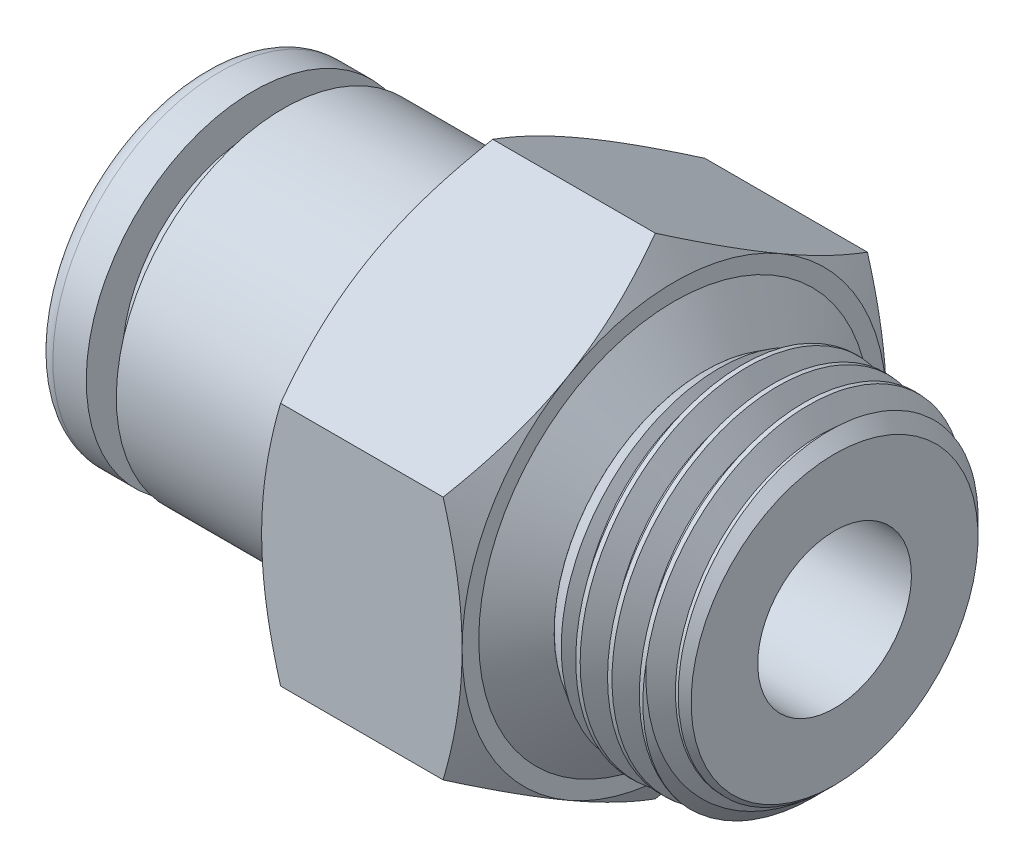
SolidWorks part; units mm, degrees
ref_plane "Front Plane" through (0, 0, 0) normal (0, 0, 1) x (1, 0, 0)
ref_plane "Top Plane" through (0, 0, 0) normal (0, 1, 0) x (1, 0, 0)
ref_plane "Right Plane" through (0, 0, 0) normal (1, 0, 0) x (0, 0, -1)
sketch "Sketch0" plane through (0, 0, 0) normal (0, 0, -1) x (-1, 0, 0)
  line L0 (0, 0) -> (-18.9, 0) construction
  line L1 (0, 5) -> (0, -5) construction
  line L2 (-13.3, 3.175) -> (-13.3, -3.175) construction
  line L3 (-14.1, 5.1435) -> (-14.1, -5.1435) construction
  line L4 (-9.45, 6.35) -> (-9.45, -6.35) construction
  line L5 (-18.9, 2.3) -> (-18.9, -2.3) construction
  point P3 (-13.3, 0)
  point P11 (-9.45, 0)
  point P16 (-14.1, 0)
sketch "Sketch1" plane through (0, 0, 0) normal (0, 0, -1) x (-1, 0, 0)
  line L0 (0, 4.5) -> (0, 3.675)
  line L1 (-0.5, 5) -> (-1.5, 5)
  line L2 (-1.5, 5) -> (-1.5, 3.925)
  line L3 (-1.5, 3.925) -> (-2.4, 3.925)
  line L4 (-2.4, 3.925) -> (-2.4, 5)
  line L5 (-2.4, 5) -> (-14.1, 5)
  line L6 (-14.1, 5.1435) -> (-14.1, -5.1435) construction
  line L7 (0, 0) -> (-18.9, 0) construction
  line L8 (-14.1, 0) -> (-9.45, 0) construction
  line L10 (0, 0) -> (-18.9, 0) construction
  line L11 (-9.45, 3.175) -> (-0.5, 3.175)
  line L12 (0, 5) -> (0, -5) construction
  line L15 (-9.45, 0) -> (-14.1, 0)
  line L16 (-14.1, 0) -> (-14.1, 5)
  line L17 (-9.45, 0) -> (-9.45, 3.175)
  line L18 (-9.45, 6.35) -> (-9.45, -6.35) construction
  arc A0 (0, 4.5) -> (-0.5, 5) centre (-0.5, 4.5) ccw
  arc A1 (-0.5, 3.175) -> (0, 3.675) centre (-0.5, 3.675) ccw
  point P15 (0, 5)
  point P19 (0, 5)
  point P25 (0, 3.175)
  dimension "R" = 0.5
  dimension "D1" = 1.5
  dimension "D3" = 7.85
  dimension "D2" = 0.9
revolve "Revolve2" add sketch "Sketch1" angle 360 about L10
ref_plane "Plane1" through (14.1, 0, 0) normal (1, 0, 0) x (0, 0, -1)
sketch "Sketch2" plane through (14.1, 0, 0) normal (1, 0, 0) x (0, 0, -1)
  circle A0 centre (0, 0) radius 5.1435
  point P5 (0, -5.1435)
extrude "Extrude1" add sketch "Sketch2" along normal up to vertex (4.8 mm away) draft 1.783 separate body up to point (18.9, 0, 0)
sketch "Sketch3" plane through (18.9, 0, 0) normal (1, 0, 0) x (0, 0, -1)
  circle A0 centre (0, 0) radius 4.9941 construction
  circle A1 centre (0, 0) radius 4.9941
curve "Helix/Spiral1" parameters "Height"=5.7236, "Pitch"=0.9236
sketch "Sketch4" plane through (0, 0, 0) normal (0, 0, -1) x (-1, 0, 0)
  line L0 (-19.7659, 5.094) -> (-19.3041, 4.2941) construction
  line L1 (-19.3041, 4.2941) -> (-18.8423, 5.094) construction
  line L2 (-18.8423, 5.094) -> (-19.7659, 5.094) construction
  line L3 (-19.7082, 4.9941) -> (-18.9, 4.9941) construction
  line L4 (-19.3041, 5.094) -> (-19.3041, 4.9941) construction
  line L5 (-19.3041, 4.9941) -> (-19.3041, 4.3941) construction
  line L6 (-19.3041, 4.3941) -> (-19.3041, 4.2941) construction
  line L7 (-19.3618, 4.3941) -> (-19.2464, 4.3941)
  line L8 (-18.8423, 5.094) -> (-19.7082, 4.9941)
  line L9 (-18.8423, 5.094) -> (-19.2464, 4.3941)
  line L10 (-19.7082, 4.9941) -> (-19.3618, 4.3941)
  line L11 (-19.3041, 4.2941) -> (-19.3041, -4.9815) construction
  line L12 (-19.3041, -4.9815) -> (-18.3809, -5.0102) construction
  line L13 (-18.3809, -5.0102) -> (-17.4577, -5.039) construction
  line L14 (-17.4577, -5.039) -> (-16.5345, -5.0677) construction
  line L15 (-16.5345, -5.0677) -> (-15.6113, -5.0964) construction
  line L16 (-18.9, -4.9941) -> (-14.1, -5.1435) construction
  dimension "D1" = 0.9236
  dimension "D2" = 0.1155
sketch "Sketch5" plane through (18.9, 0, 0) normal (1, 0, 0) x (0, 0, -1)
  circle A0 centre (0, 0) radius 4.2941
extrude "Extrude2" cut sketch "Sketch5" against normal up to vertex (4.8 mm away) draft 45 flip side to cut up to point (14.1, 0, 0)
sweep "Cut-Sweep1" cut profiles "Sketch4" path "Helix/Spiral1"
sketch "Sketch5.5" plane through (0, 0, 0) normal (0, 0, 1) x (1, 0, 0)
  line L0 (14.1, -5.1435) -> (15.0232, -5.1148)
  line L1 (19.3041, -4.9815) -> (18.3809, -5.0102) construction
  line L2 (15.0232, -5.1148) -> (15.9464, -5.086)
  line L3 (15.9464, -5.086) -> (15.0232, -4.5148)
  line L4 (15.0232, -4.5148) -> (15.0232, -5.1148) construction
  line L5 (19.3041, 4.9941) -> (19.3041, 4.3941) construction
  line L6 (15.0232, -4.5148) -> (14.1, -4.5436)
  line L7 (14.1, -4.5436) -> (14.1, -5.1435)
  line L8 (14.1, 0) -> (19.3041, 0) construction
  line L9 (14.1, -5.1435) -> (14.1, 5.1435) construction
  line L10 (19.3041, 4.2941) -> (19.3041, -4.9815) construction
revolve "Cut-Revolve1" cut sketch "Sketch5.5" angle 360 about L8
ref_plane "Plane2" through (14.1, 0, 0) normal (1, 0, 0) x (0, 0, -1)
sketch "Sketch6" plane through (14.1, 0, 0) normal (1, 0, 0) x (0, 0, -1)
  circle A0 centre (0, 0) radius 3.175
  circle A2 centre (0, 0) radius 5.1435
  circle A3 centre (0, 0) radius 5.1435
  dimension "D1" = 0
extrude "Extrude3" add sketch "Sketch6" against normal blind 3 draft 45
sketch "Sketch7" plane through (18.9, 0, 0) normal (1, 0, 0) x (0, 0, -1)
  circle A0 centre (0, 0) radius 2.3
extrude "Extrude4" cut sketch "Sketch7" against normal through all
sketch "Sketch8" plane through (14.1, 0, 0) normal (1, 0, 0) x (0, 0, -1)
  line L1 (0, 7.3323) -> (-6.35, 3.6662)
  line L2 (-6.35, 3.6662) -> (-6.35, -3.6662)
  line L3 (-6.35, -3.6662) -> (0, -7.3323)
  line L4 (0, -7.3323) -> (6.35, -3.6662)
  line L5 (6.35, -3.6662) -> (6.35, 3.6662)
  line L6 (6.35, 3.6662) -> (0, 7.3323)
  circle A0 centre (0, 0) radius 6.35 construction
  circle A3 centre (0, 0) radius 5
extrude "Extrude5" add sketch "Sketch8" against normal blind 6
sketch "Sketch9" plane through (14.1, 0, 0) normal (1, 0, 0) x (0, 0, -1)
  circle A0 centre (0, 0) radius 6.35 construction
  circle A1 centre (0, 0) radius 6.35
extrude "Extrude6" cut sketch "Sketch9" against normal up to vertex (6 mm away) draft 60 flip side to cut up to point (8.1, 7.3323, 0)
sketch "Sketch10" plane through (8.1, 0, 0) normal (-1, 0, 0) x (0, 0, 1)
  circle A1 centre (0, 0) radius 6.35
  circle A2 centre (0, 0) radius 6.35
  dimension "D1" = 0
extrude "Extrude7" cut sketch "Sketch10" against normal up to vertex (6 mm away) draft 60 flip side to cut up to point (14.1, 7.3323, 0)
sketch "Sketch12" plane through (0, 0, 0) normal (0, 0, 1) x (1, 0, 0)
  line L0 (0, 0) -> (18.9, 0) construction
  line L1 (0, 4.5) -> (0, -4.5) construction
  line L3 (15.0232, -4.5148) -> (14.1, -4.5436) construction
  line L8 (14.1, -5.1435) -> (14.1, -5.8516)
  line L9 (14.5234, -4.5304) -> (14.1, -5.1435)
  line L10 (14.5234, -4.5304) -> (15.0232, -4.5148)
  line L11 (14.1, -5.8516) -> (15.0232, -4.5148)
  dimension "D1" = 0.5
revolve "Revolve3" add sketch "Sketch12" angle 360 about L0
equation "\"Height@Helix/Spiral1\" = \"Pitch@Helix/Spiral1\" + \"Thread Length@Sketch0\""
equation "\"D1@Sketch4\" = \"Pitch@Helix/Spiral1\""
equation "\"D2@Sketch4\" = \"D1@Sketch4\" * 1 / 8"
